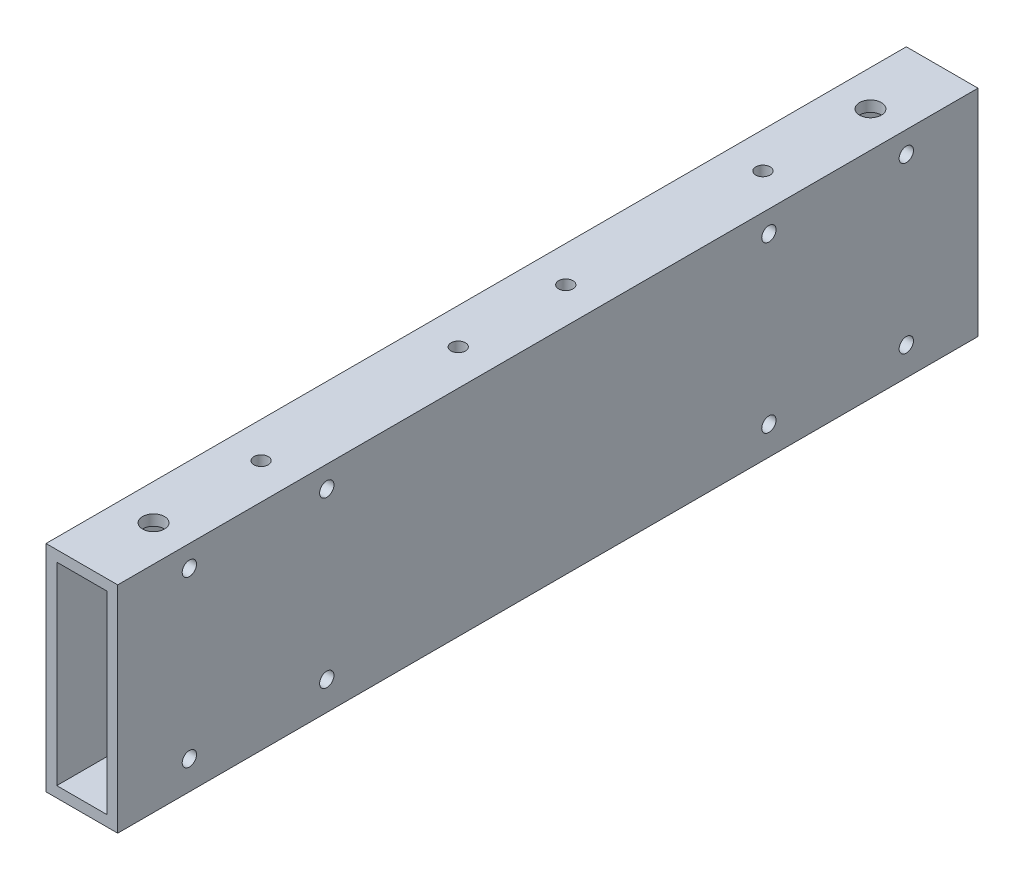
SolidWorks part; units mm, degrees
ref_plane "前视基准面" through (0, 0, 0) normal (0, 0, 1) x (1, 0, 0)
ref_plane "上视基准面" through (0, 0, 0) normal (0, 1, 0) x (1, 0, 0)
ref_plane "右视基准面" through (0, 0, 0) normal (1, 0, 0) x (0, 0, -1)
sketch "草图1" plane through (0, 0, 0) normal (0, 0, 1) x (1, 0, 0)
  line L1 (-36.6168, 25.7879) -> (-16.6168, 25.7879)
  line L2 (-36.6168, 25.7879) -> (-36.6168, -34.2121)
  line L3 (-36.6168, -34.2121) -> (-16.6168, -34.2121)
  line L4 (-16.6168, 25.7879) -> (-16.6168, -34.2121)
  dimension "D1" = 60
  dimension "D2" = 20
extrude "凸台-拉伸1" add sketch "草图1" along normal blind 240
sketch "草图2" plane through (0, 0, 240) normal (0, 0, 1) x (1, 0, 0)
  line L0 (-36.6168, 25.7879) -> (-36.6168, -34.2121) construction
  line L1 (-33.6168, 22.7879) -> (-19.6168, 22.7879)
  line L2 (-33.6168, 22.7879) -> (-33.6168, -31.2121)
  line L3 (-33.6168, -31.2121) -> (-19.6168, -31.2121)
  line L4 (-19.6168, 22.7879) -> (-19.6168, -31.2121)
  line L5 (-16.6168, -34.2121) -> (-16.6168, 25.7879) construction
  line L6 (-36.6168, -34.2121) -> (-16.6168, -34.2121) construction
  line L7 (-16.6168, 25.7879) -> (-36.6168, 25.7879) construction
  dimension "D1" = 3
  dimension "D2" = 3
  dimension "D3" = 3
  dimension "D4" = 3
extrude "切除-拉伸1" cut sketch "草图2" against normal through all
sketch "草图3" plane through (-16.6168, 0, 0) normal (1, 0, 0) x (0, 0, -1)
  line L0 (-240, -34.2121) -> (-240, 25.7879) construction
  line L1 (-240, 25.7879) -> (0, 25.7879) construction
  line L2 (-240, -34.2121) -> (0, -34.2121) construction
  line L3 (-120, 25.7879) -> (-120, -34.2121) construction
  circle A0 centre (-220, 19.7879) radius 2
  circle A1 centre (-20, 19.7879) radius 2
  circle A2 centre (-181.67, 19.7879) radius 2
  circle A3 centre (-220, -26.2121) radius 2
  circle A4 centre (-181.67, -26.2121) radius 2
  circle A5 centre (-20, -26.2121) radius 2
  circle A6 centre (-58.33, -26.2121) radius 2
  circle A7 centre (-58.33, 19.7879) radius 2
  dimension "D1" = 4
  dimension "D2" = 4
  dimension "D3" = 4
  dimension "D4" = 20
  dimension "D5" = 200
  dimension "D6" = 38.33
  dimension "D7" = 6
  dimension "D8" = 4
  dimension "D9" = 4
  dimension "D10" = 4
  dimension "D11" = 8
  dimension "D12" = 8
  dimension "D13" = 8
  dimension "D14" = 38.33
extrude "切除-拉伸2" cut sketch "草图3" against normal blind 240
sketch "草图4" plane through (0, 25.7879, 0) normal (0, 1, 0) x (1, 0, 0)
  line L0 (-16.6168, -240) -> (-36.6168, -240) construction
  line L1 (-36.6168, -240) -> (-36.6168, 0) construction
  line L2 (-16.6168, 0) -> (-36.6168, 0) construction
  line L3 (-16.6168, -240) -> (-16.6168, 0) construction
  line L4 (-16.6168, -120) -> (-36.6168, -120) construction
  circle A0 centre (-26.6168, -220) radius 3.05
  circle A1 centre (-26.6168, -190) radius 2
  circle A2 centre (-26.6168, -135) radius 2
  circle A3 centre (-26.6168, -50) radius 2
  circle A4 centre (-26.6168, -20) radius 3.05
  circle A5 centre (-26.6168, -105) radius 2
  dimension "D1" = 6.1
  dimension "D2" = 20
  dimension "D3" = 10
  dimension "D4" = 4
  dimension "D5" = 30
  dimension "D6" = 55
  dimension "D7" = 30
  dimension "D8" = 6.1
  dimension "D9" = 4
  dimension "D10" = 4
  dimension "D11" = 4
  dimension "D12" = 30
  dimension "D13" = 55
  dimension "D14" = 20
extrude "切除-拉伸3" cut sketch "草图4" against normal through all
